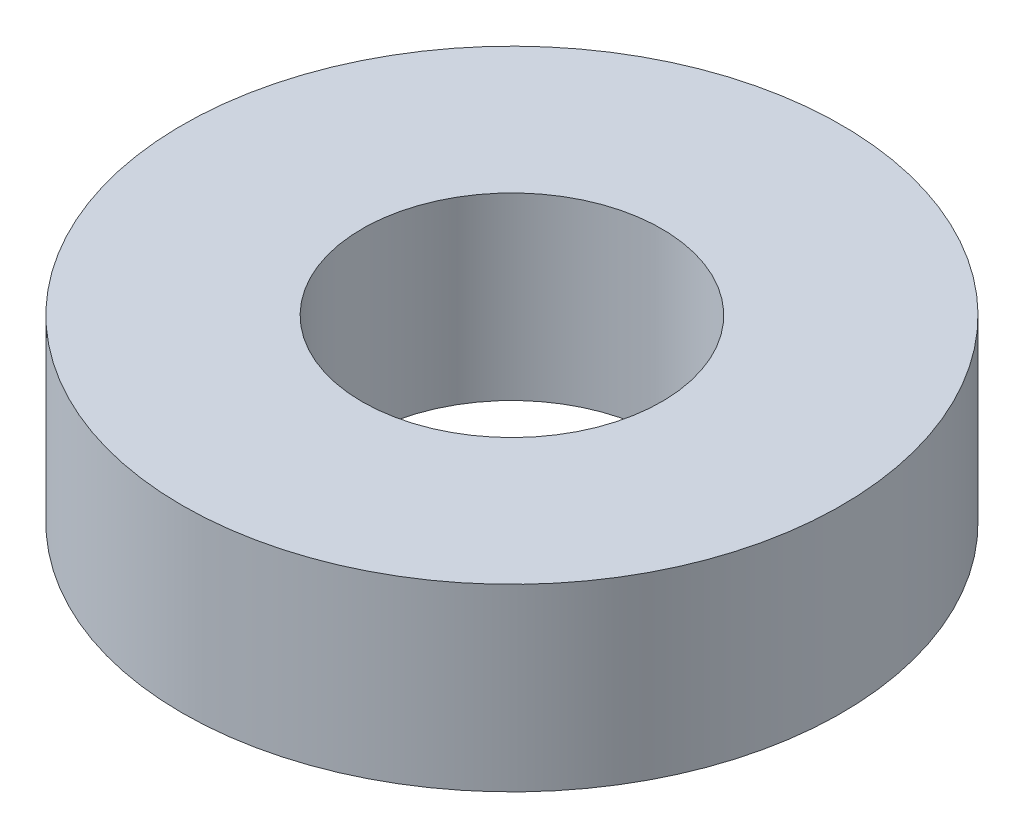
SolidWorks part; units mm, degrees
material "不锈钢 (铁素体)"
ref_plane "前视基准面" through (0, 0, 0) normal (0, 0, 1) x (1, 0, 0)
ref_plane "上视基准面" through (0, 0, 0) normal (0, 1, 0) x (1, 0, 0)
ref_plane "右视基准面" through (0, 0, 0) normal (1, 0, 0) x (0, 0, -1)
sketch "草图1" plane through (0, 0, 0) normal (0, 1, 0) x (1, 0, 0)
  circle A0 centre (0, 0) radius 11
  circle A1 centre (0, 0) radius 5
  dimension "D1" = 10
  dimension "D2" = 22
extrude "凸台-拉伸1" add sketch "草图1" along normal blind 6
